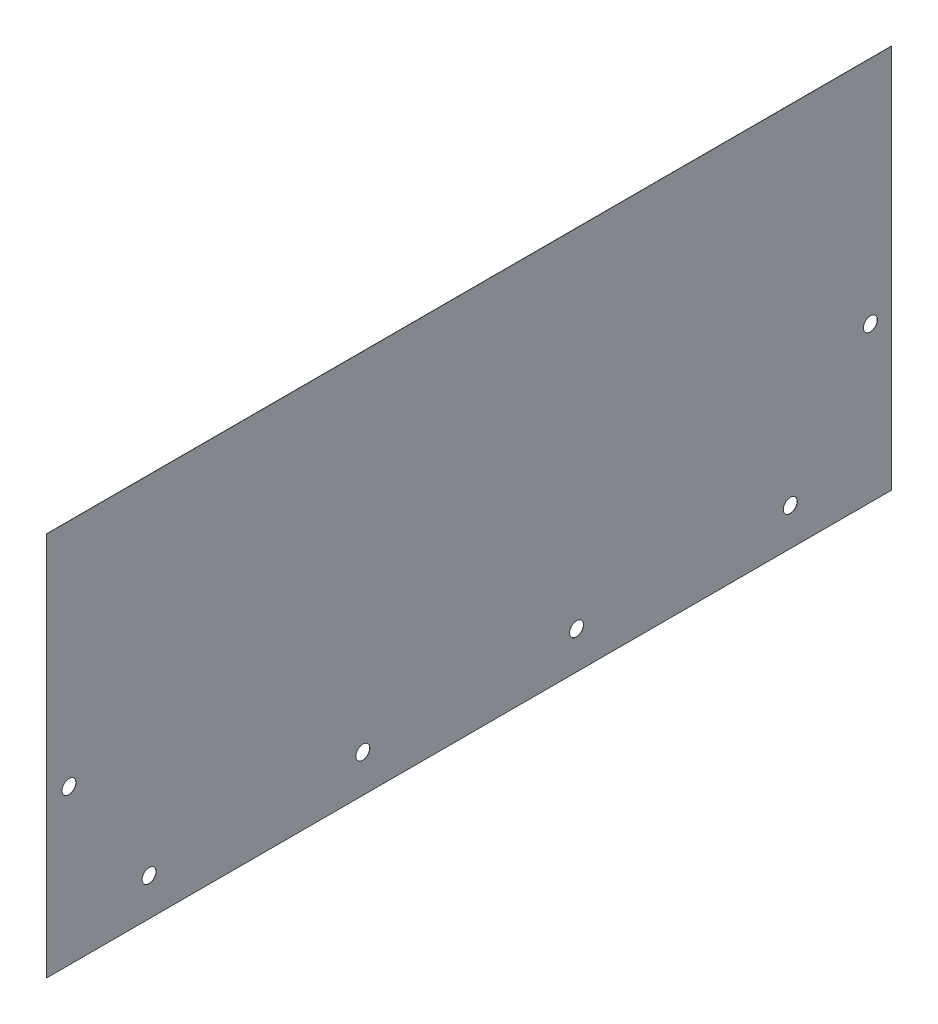
SolidWorks part; units mm, degrees
material "Acrylic (Medium-high impact)"
ref_plane "Front Plane" through (0, 0, 0) normal (0, 0, 1) x (1, 0, 0)
ref_plane "Top Plane" through (0, 0, 0) normal (0, 1, 0) x (1, 0, 0)
ref_plane "Right Plane" through (0, 0, 0) normal (1, 0, 0) x (0, 0, -1)
sketch "Sketch1" plane through (0, 0, 0) normal (1, 0, 0) x (0, 0, -1)
  line L0 (-251.1933, 404.8633) -> (-251.1933, 407.9367) construction
  line L1 (251.1933, -404.8633) -> (-251.1933, -404.8633)
  line L2 (251.1933, -404.8633) -> (251.1933, 404.8633)
  line L3 (251.1933, 404.8633) -> (-251.1933, 404.8633)
  line L4 (-251.1933, -404.8633) -> (-251.1933, 404.8633)
  line L5 (251.1933, -404.8633) -> (-251.1933, 404.8633) construction
  line L6 (251.1933, 404.8633) -> (-251.1933, -404.8633) construction
  point P0 (0, 0)
  dimension "D1" = 502.3866
  dimension "D2" = 3.0734
  dimension "D3" = 812.8
extrude "SidePanel" add sketch "Sketch1" along normal blind 0.127
sketch "Sketch2" plane through (0.127, 0, 0) normal (1, 0, 0) x (0, 0, -1)
  line L3 (190.9699, -392.1633) -> (190.9699, -373.1133) construction
  line L5 (-251.1933, -404.8633) -> (251.1933, -404.8633) construction
  line L9 (251.1933, -404.8633) -> (251.1933, 404.8633) construction
  circle A1 centre (190.9699, -382.6383) radius 4.1656
  dimension "D8" = 8.3312
  dimension "D4" = 19.05
  dimension "D5" = 12.7
  dimension "D9" = 60.2234
extrude "TopBottomHoleMaster" cut sketch "Sketch2" against normal through all
pattern_linear "LPattern1" count 4 spacing 127.0677 along (0, 0, 1) of "TopBottomHoleMaster"
sketch "Sketch3" plane through (0.127, 0, 0) normal (1, 0, 0) x (0, 0, -1)
  line L0 (251.1933, 322.2117) -> (248.1199, 322.2117) construction
  line L1 (251.1933, -404.8633) -> (251.1933, 404.8633) construction
  line L2 (248.1199, 322.2117) -> (229.0699, 322.2117) construction
  line L3 (251.1933, 404.8633) -> (251.1933, 407.9367) construction
  line L4 (251.1933, 404.8633) -> (-251.1933, 404.8633) construction
  line L5 (-250.5583, 322.2117) -> (-247.3833, 322.2117) construction
  line L6 (-250.5583, 322.2117) -> (-253.7333, 322.2117) construction
  line L8 (-247.3833, 322.2117) -> (-228.3333, 322.2117) construction
  line L11 (-253.7333, 322.2117) -> (-256.8067, 322.2117) construction
  line L12 (251.1933, -404.8633) -> (251.1933, 404.8633) construction
  circle A0 centre (-237.8583, 322.2117) radius 4.1656
  circle A1 centre (238.5949, 322.2117) radius 4.1656
  dimension "D5" = 8.3312
  dimension "D1" = 3.0734
  dimension "D2" = 19.05
  dimension "D3" = 3.0734
  dimension "D4" = 85.725
  dimension "D6" = 3.175
  dimension "D8" = 3.0734
  dimension "D9" = 508
extrude "RearHolesMaster" cut sketch "Sketch3" against normal through all
pattern_linear "LPattern2" count 4 spacing 211.7344 along (0, -1, 0) of "RearHolesMaster"
sketch "Sketch4" plane through (0, 0, 0) normal (-1, 0, 0) x (0, 0, 1)
  line L1 (-251.1933, 404.8633) -> (251.1933, 404.8633)
  line L2 (-251.1933, 404.8633) -> (-251.1933, -176.2633)
  line L3 (-251.1933, -176.2633) -> (251.1933, -176.2633)
  line L4 (251.1933, 404.8633) -> (251.1933, -176.2633)
  line L5 (-251.1933, 404.8633) -> (251.1933, -176.2633) construction
  line L6 (-251.1933, -176.2633) -> (251.1933, 404.8633) construction
  line L7 (251.1933, -404.8633) -> (-251.1933, -404.8633) construction
  point P0 (0, 114.3)
  dimension "D1" = 228.6
extrude "Cut-Extrude1" cut sketch "Sketch4" against normal through all
equation "\"Height\"= 32in"
equation "\"Width\"= 23in"
equation "\"Depth\"= 20in"
equation "\"Plexi\"= .121in"
equation "\"Cutwidth\"= .016in"
equation "\"Earsize\"= 1in + \"Cutwidth\" /2"
equation "\"Slotsize\" = 1in - \"CutWidth\" / 2"
equation "\"InnerWidth\" = \"Width\" - 2* \"Plexi\""
equation "\"InnerHeight\" = \"Height\" -2 * \"Plexi\""
equation "\"InnerDepth\" = \"Depth\" - 2*\"Plexi\""
equation "\"RearHoleSpacing\" = (\"Width\" - 2*\"RearHolesBorder\") / (\"RearNumHoles\"-1)"
equation "\"RivetDia\" = .228in"
equation "\"SlotDepth\" = \"Plexi\" + 0.75in + .005in"
equation "\"SideSlotWidth\"   = \"Plexi\"+.005in"
equation "\"SidePanelVertSpacing\" = (\"Height\"-2*(1.75-\"Plexi\")) / 5"
equation "\"BottomPanelSideHoleSpacing\" = (\"InnerDepth\"-2*(1.75-\"Plexi\")) / 4"
equation "\"D1@Sketch1\"=\"TopDepth\""
equation "\"D2@Sketch1\"=\"Plexi\""
equation "\"D1@SidePanel\"=\"Plexi\""
equation "\"MagnetThickness\"= 0.125in"
equation "\"MagnetDiameter\"= 12mm"
equation "\"DoorPlexi\" = \"Plexi\""
equation "\"Boxsize\" = .75in"
equation "\"Boxinner\" = .625in"
equation "\"CornerCube\" = 0.75in"
equation "\"FingerLength\" = 1.125in"
equation "\"RearNumHoles\" = 4"
equation "\"RearHolesBorder\" = 2.25"
equation "\"RearBarLength\" = (\"InnerWidth\"-2*\"CornerCube\")"
equation "\"RearTopNumHoles\" = 4"
equation "\"RearTopHolesBorder\" = 3.1"
equation "\"RearTopHolesSpacing\" = (\"Width\" - 2*\"RearTopHolesBorder\") / (\"RearTopNumHoles\"-1)"
equation "\"SideTopNumHoles\" = 4"
equation "\"SideTopHoleOffset\"=\"CornerCube\"+\"FingerLength\"+\"Plexi\"+.5"
equation "\"SideTopHoleSpacing\" = (\"TopBarDepth\"-2*\"SideTopHoleOffset\") / (\"SideTopNumHoles\"-1)"
equation "\"SideHorizNumHoles\" = 4"
equation "\"SideHorizHoleBorder\" = 1.50"
equation "\"SideHorizHoleSpacing\" = (\"TopBarDepth\"-2*\"SideHorizHoleBorder\") / (\"SideHorizNumHoles\"-1)"
equation "\"SideVertNumHoles\" = 4"
equation "\"SideVertHolesBorder\" = \"CornerCube\"+\"FingerLength\"+1.50"
equation "\"SideVertHoleSpacing\" = (\"InnerHeight\" - 2*\"SideVertHolesBorder\") / (\"SideVertNumHoles\"-1)"
equation "\"FrontDoorGap\" = .1in"
equation "\"TopDepth\" = \"Depth\"-\"DoorPlexi\"-\"FrontDoorGap\""
equation "\"TopBarDepth\" = \"Depth\"-\"DoorPlexi\"-\"Plexi\"-2*\"MagnetThickness\"-2*\"CornerCube\""
equation "\"D3@LPattern1\"=\"SideHorizHoleSpacing\""
equation "\"D1@LPattern1\"=\"SideHorizNumHoles\""
equation "\"D1@Sketch3\"=\"Plexi\""
equation "\"D2@Sketch3\"=\"Boxsize\""
equation "\"D3@Sketch3\"=\"Plexi\""
equation "\"D4@Sketch3\"=\"SideVertHolesBorder\""
equation "\"D5@Sketch3\"=\"RivetDia\"+.1"
equation "\"D3@LPattern2\"=\"SideVertHoleSpacing\""
equation "\"D1@LPattern2\"=\"SideVertNumHoles\""
equation "\"BasePlateThickness\" = 0.5in"
equation "\"SideVertBarLength\"=\"Height\"-\"BasePlateThickness\"-2*\"CornerCube\"-\"Plexi\""
equation "\"RearSideVertNumHoles\" = 4"
equation "\"RearSideVertHolesBorder\" = 2.4"
equation "\"RearSideVertHoleSpacing\" = (\"InnerHeight\" - 2*\"RearSideVertHolesBorder\") / (\"RearSideVertNumHoles\"-1)"
equation "\"D3@Sketch1\"=\"Height\""
equation "\"D6@Sketch3\"=\"MagnetThickness\""
equation "\"D8@Sketch3\"=\"DoorPlexi\""
equation "\"D9@Sketch3\"=\"Depth\""
equation "\"D8@Sketch2\"=\"RivetDia\"+.1"
equation "\"D9@Sketch2\"=\"Plexi\"+\"Boxsize\"+\"SideHorizHoleBorder\""
